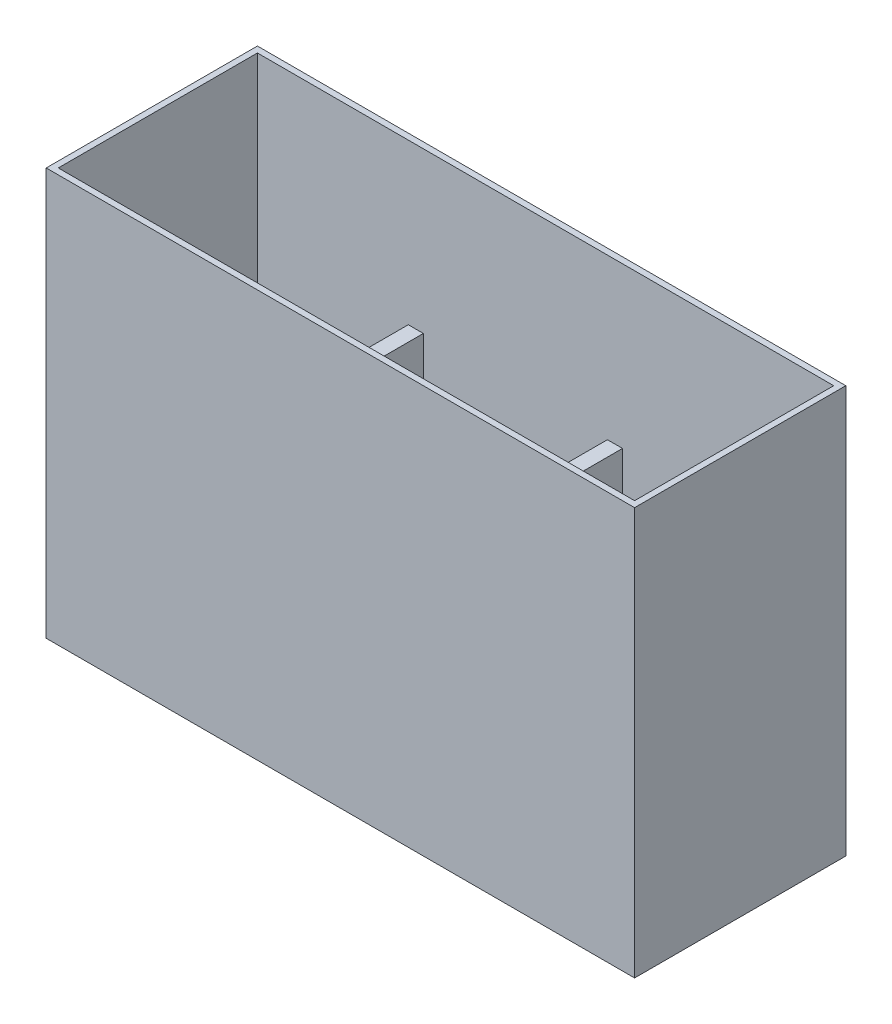
SolidWorks part; units mm, degrees
material "ABS"
ref_plane "Front Plane" through (0, 0, 0) normal (0, 0, 1) x (1, 0, 0)
ref_plane "Top Plane" through (0, 0, 0) normal (0, 1, 0) x (1, 0, 0)
ref_plane "Right Plane" through (0, 0, 0) normal (1, 0, 0) x (0, 0, -1)
sketch "Sketch1" plane through (0, 0, 0) normal (0, 1, 0) x (1, 0, 0)
  line L1 (0, 0) -> (247.65, 0)
  line L2 (0, 0) -> (0, -88.9)
  line L3 (0, -88.9) -> (247.65, -88.9)
  line L4 (247.65, 0) -> (247.65, -88.9)
  dimension "D1" = 247.65
  dimension "D2" = 88.9
extrude "Boss-Extrude1" add sketch "Sketch1" along normal blind 171.45
shell "Shell1" thickness 2.54
sketch "Sketch2" plane through (0, 2.54, 0) normal (0, 1, 0) x (1, 0, 0)
  line L0 (245.11, -73.66) -> (156.21, -73.66)
  line L1 (245.11, -86.36) -> (245.11, -2.54) construction
  line L2 (156.21, -73.66) -> (156.21, -86.36)
  line L3 (2.54, -86.36) -> (245.11, -86.36) construction
  line L4 (245.11, -67.31) -> (149.86, -67.31)
  line L5 (245.11, -86.36) -> (245.11, -2.54) construction
  line L6 (149.86, -67.31) -> (149.86, -86.36)
  line L7 (2.54, -86.36) -> (245.11, -86.36) construction
  line L8 (149.86, -86.36) -> (156.21, -86.36)
  line L9 (245.11, -67.31) -> (245.11, -73.66)
  dimension "D1" = 88.9
  dimension "D2" = 12.7
  dimension "D3" = 6.35
  dimension "D4" = 6.35
extrude "Boss-Extrude2" add sketch "Sketch2" along normal blind 101.6
sketch "Sketch4" plane through (0, 0, 67.31) normal (0, 0, -1) x (-1, 0, 0)
  line L0 (-245.11, 104.14) -> (-149.86, 104.14) construction
  line L1 (-149.86, 104.14) -> (-149.86, 2.54) construction
  circle A0 centre (-197.485, 104.14) radius 25.4
  dimension "D1" = 50.8
  dimension "D2" = 47.625
extrude "Cut-Extrude1" cut sketch "Sketch4" against normal up to next
sketch "Sketch5" plane through (0, 2.54, 0) normal (0, 1, 0) x (1, 0, 0)
  line L0 (156.21, -67.31) -> (156.21, -2.54)
  line L1 (172.085, -67.31) -> (149.86, -67.31) construction
  line L2 (245.11, -2.54) -> (2.54, -2.54) construction
  line L3 (156.21, -2.54) -> (149.86, -2.54)
  line L4 (245.11, -2.54) -> (2.54, -2.54) construction
  line L5 (149.86, -2.54) -> (149.86, -67.31)
  line L6 (149.86, -67.31) -> (156.21, -67.31)
  line L7 (66.04, -2.54) -> (66.04, -86.36)
  line L8 (2.54, -86.36) -> (149.86, -86.36) construction
  line L9 (66.04, -86.36) -> (72.39, -86.36)
  line L10 (72.39, -86.36) -> (72.39, -2.54)
  line L11 (72.39, -2.54) -> (66.04, -2.54)
  line L12 (2.54, -2.54) -> (2.54, -86.36) construction
  dimension "D1" = 63.5
  dimension "D2" = 6.35
  dimension "D3" = 6.35
extrude "Boss-Extrude3" add sketch "Sketch5" along normal up to surface (101.6 mm away) up to face at (159.385, 104.14, 75.7767)
